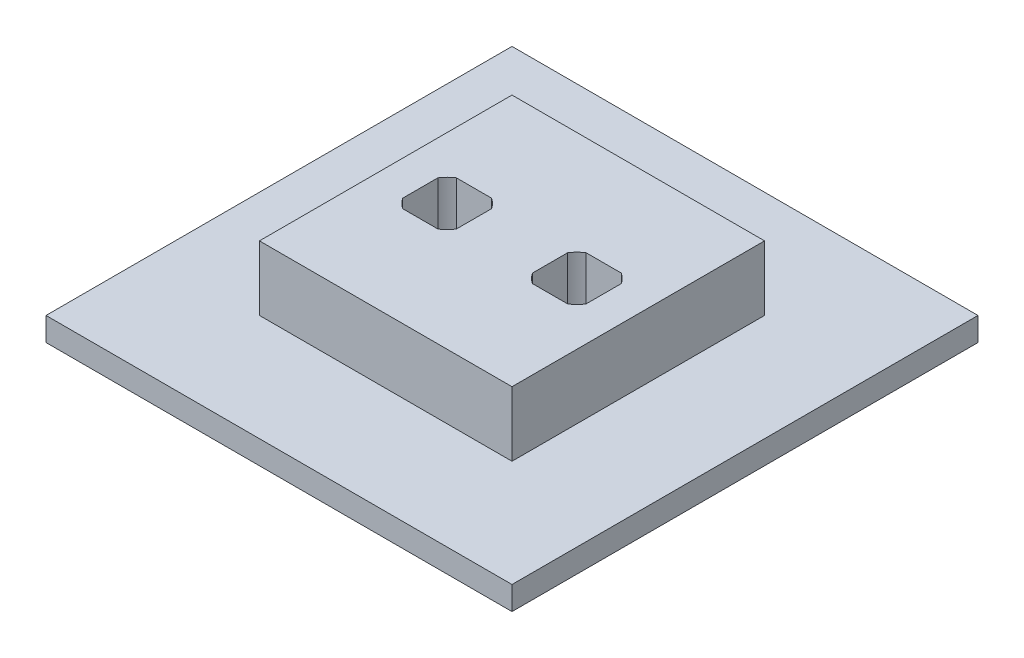
SolidWorks part; units mm, degrees
ref_plane "Front Plane" through (0, 0, 0) normal (0, 0, 1) x (1, 0, 0)
ref_plane "Top Plane" through (0, 0, 0) normal (0, 1, 0) x (1, 0, 0)
ref_plane "Right Plane" through (0, 0, 0) normal (1, 0, 0) x (0, 0, -1)
sketch "Sketch1" plane through (0, 0, 0) normal (0, 1, 0) x (1, 0, 0)
  line L1 (0, 0) -> (79.375, 0)
  line L2 (0, 0) -> (0, 79.375)
  line L3 (0, 79.375) -> (79.375, 79.375)
  line L4 (79.375, 0) -> (79.375, 79.375)
  dimension "D1" = 79.375
extrude "Boss-Extrude1" add sketch "Sketch1" along normal blind 4
sketch "Sketch2" plane through (0, 4, 0) normal (0, 1, 0) x (1, 0, 0)
  line L0 (79.375, 79.375) -> (0, 0) construction
  line L1 (18.1775, 18.1775) -> (61.1975, 18.1775)
  line L2 (18.1775, 18.1775) -> (18.1775, 61.1975)
  line L3 (18.1775, 61.1975) -> (61.1975, 61.1975)
  line L4 (61.1975, 18.1775) -> (61.1975, 61.1975)
  line L5 (18.1775, 39.6875) -> (61.1975, 39.6875) construction
  line L6 (28.6385, 45.1485) -> (50.7365, 45.1485) construction
  circle A0 centre (28.6385, 39.6875) radius 5.461
  circle A1 centre (50.7365, 39.6875) radius 5.461
  point P13 (39.6875, 39.6875)
  point P18 (39.6875, 45.1485)
  point P21 (39.6875, 39.6875)
  dimension "D2" = 22.098
  dimension "D1" = 10.922
  dimension "D3" = 5
extrude "Boss-Extrude2" add sketch "Sketch2" along normal blind 11
sketch "Sketch3" plane through (0, 15, 0) normal (0, 1, 0) x (1, 0, 0)
  circle A0 centre (28.6385, 39.6875) radius 5.461
  circle A1 centre (50.7365, 39.6875) radius 5.461
  circle A2 centre (28.6385, 39.6875) radius 5.461 construction
  circle A3 centre (50.7365, 39.6875) radius 5.461 construction
extrude "Cut-Extrude1" cut sketch "Sketch3" against normal through all both and the other way through all
sketch "Sketch4" plane through (0, 15, 0) normal (0, 1, 0) x (1, 0, 0)
  line L1 (24.0775, 35.1265) -> (33.1995, 35.1265)
  line L2 (24.0775, 35.1265) -> (24.0775, 44.2485)
  line L3 (24.0775, 44.2485) -> (33.1995, 44.2485)
  line L4 (33.1995, 35.1265) -> (33.1995, 44.2485)
  line L5 (46.1755, 44.2485) -> (55.2975, 44.2485)
  line L6 (46.1755, 44.2485) -> (46.1755, 35.1265)
  line L7 (46.1755, 35.1265) -> (55.2975, 35.1265)
  line L8 (55.2975, 44.2485) -> (55.2975, 35.1265)
  line L9 (20.3252, 47.7821) -> (59.1308, 47.7821)
  line L10 (20.3252, 47.7821) -> (20.3252, 29.8799)
  line L11 (20.3252, 29.8799) -> (59.1308, 29.8799)
  line L12 (59.1308, 47.7821) -> (59.1308, 29.8799)
  circle A1 centre (28.6385, 39.6875) radius 5.461 construction
  circle A2 centre (50.7365, 39.6875) radius 5.461 construction
  dimension "D1" = 0.9
  dimension "D2" = 0.9
  dimension "D3" = 0.9
  dimension "D4" = 0.9
extrude "Boss-Extrude3" add sketch "Sketch4" against normal up to surface (15 mm away) up to face at (28.6385, 0, -34.2265)
